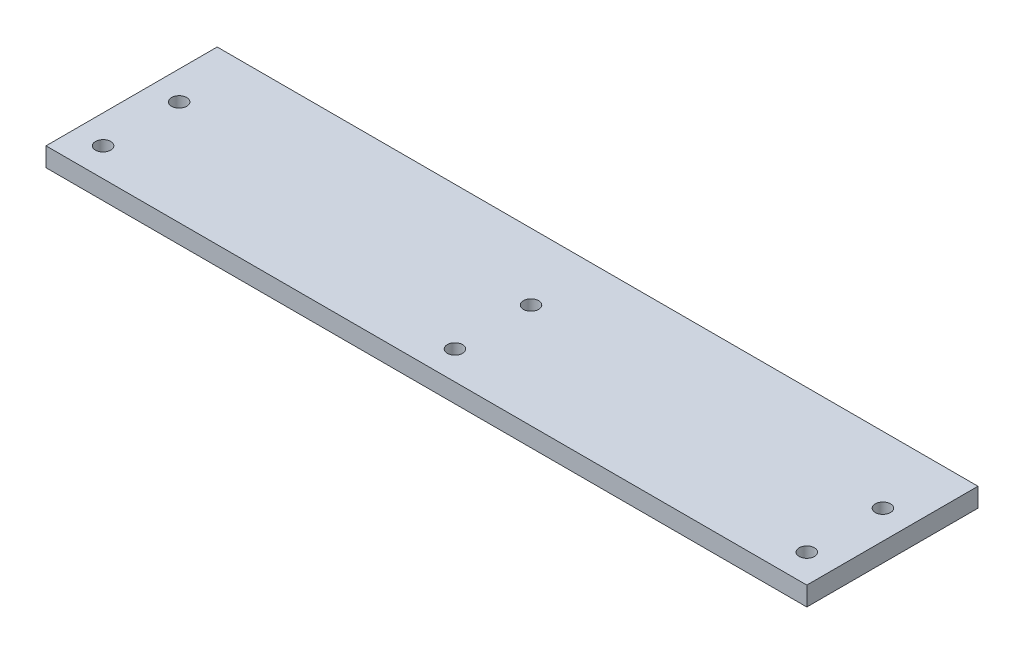
SolidWorks part; units mm, degrees
ref_plane "Front Plane" through (0, 0, 0) normal (0, 0, 1) x (1, 0, 0)
ref_plane "Top Plane" through (0, 0, 0) normal (0, 1, 0) x (1, 0, 0)
ref_plane "Right Plane" through (0, 0, 0) normal (1, 0, 0) x (0, 0, -1)
sketch "Sketch1" plane through (0, 0, 0) normal (0, 1, 0) x (1, 0, 0)
  line L1 (63.5, -12.7) -> (-63.5, -12.7)
  line L2 (63.5, -12.7) -> (63.5, 12.7)
  line L3 (63.5, 12.7) -> (-63.5, 12.7)
  line L4 (-63.5, -12.7) -> (-63.5, 12.7)
  line L5 (63.5, -12.7) -> (-63.5, 12.7) construction
  line L6 (63.5, 12.7) -> (-63.5, -12.7) construction
  line L7 (63.5, -25.4) -> (63.5, 0) [skipped]
  line L8 (-63.5, 12.7) -> (63.5, 12.7)
  line L9 (-63.5, 12.7) -> (-63.5, 15.875)
  line L10 (-63.5, 15.875) -> (63.5, 15.875)
  line L11 (63.5, 12.7) -> (63.5, 15.875)
  circle A0 centre (-58.7375, 4.7625) radius 1.27
  circle A1 centre (0, 4.7625) radius 1.27
  circle A2 centre (58.7375, 4.7625) radius 1.27
  circle A3 centre (-58.7375, -7.9375) radius 1.27
  circle A4 centre (0, -7.9375) radius 1.27
  circle A5 centre (58.7375, -7.9375) radius 1.27
  point P0 (0, 0)
  dimension "D2" = 2.54
  dimension "D1" = 127
  dimension "D3" = 4.7625
  dimension "D4" = 4.7625
  dimension "D5" = 25.4
  dimension "D6" = 7.9375
  dimension "D8" = 4.7625
  dimension "D9" = 3.175
  dimension "D7" = 2
extrude "Boss-Extrude1" add sketch "Sketch1" along normal blind 3.175 contours L4 L1 L2 L3 A5 A4 A3 A2 A1 A0 | L3 L11 L10 L9
sketch "Sketch2" plane through (0, 3.175, 0) normal (0, 1, 0) x (1, 0, 0)
  line L0 (-63.5, -12.7) -> (-63.5, 15.875) construction
